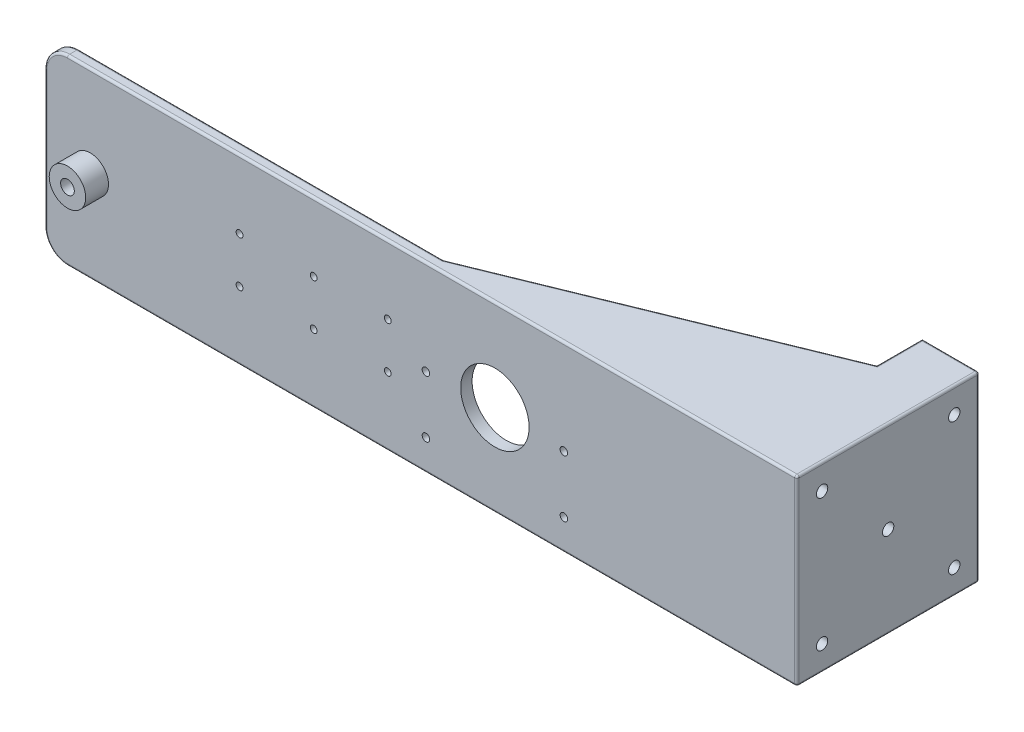
SolidWorks part; units mm, degrees
ref_plane "前视基准面" through (0, 0, 0) normal (0, 0, 1) x (1, 0, 0)
ref_plane "上视基准面" through (0, 0, 0) normal (0, 1, 0) x (1, 0, 0)
ref_plane "右视基准面" through (0, 0, 0) normal (1, 0, 0) x (0, 0, -1)
sketch "草图1" plane through (0, 0, 0) normal (0, 0, 1) x (1, 0, 0)
  line L1 (165, -40) -> (-165, -40)
  line L2 (165, -40) -> (165, 40)
  line L3 (165, 40) -> (-165, 40)
  line L4 (-165, -40) -> (-165, 40)
  line L5 (165, -40) -> (-165, 40) construction
  line L6 (165, 40) -> (-165, -40) construction
  point P0 (0, 0)
  dimension "D1" = 80
  dimension "D2" = 330
extrude "凸台-拉伸1" add sketch "草图1" along normal blind 5
sketch "草图2" plane through (0, 0, 5) normal (0, 0, 1) x (1, 0, 0)
  line L0 (-165, 40) -> (-165, -40) construction
  circle A0 centre (-145, 0) radius 5
  dimension "D1" = 10
  dimension "D2" = 20
extrude "切除-拉伸1" cut sketch "草图2" against normal blind 5
sketch "草图3" plane through (0, 0, 5) normal (0, 0, 1) x (1, 0, 0)
  circle A0 centre (-45, 0) radius 4
  dimension "D2" = 8
extrude "切除-拉伸2" cut sketch "草图3" against normal blind 10
sketch "草图4" plane through (0, 0, 5) normal (0, 0, 1) x (1, 0, 0)
  line L1 (-3, -10) -> (-91, -10)
  line L2 (-3, -10) -> (-3, 10)
  line L3 (-3, 10) -> (-91, 10)
  line L4 (-91, -10) -> (-91, 10)
  line L5 (-3, -10) -> (-91, 10) construction
  line L6 (-3, 10) -> (-91, -10) construction
  line L7 (-165, 40) -> (-165, -40) construction
  point P0 (-47, 0)
  dimension "D1" = 162
  dimension "D2" = 20
  dimension "D3" = 88
extrude "凸台-拉伸2" add sketch "草图4" along normal blind 10
sketch "草图5" plane through (0, 0, 5) normal (0, 0, 1) x (1, 0, 0)
  line L1 (-165, 40) -> (-165, -40) construction
  circle A0 centre (32.5, 0) radius 15
  dimension "D1" = 30
  dimension "D2" = 197.5
extrude "切除-拉伸3" cut sketch "草图5" against normal blind 10
sketch "草图6" plane through (0, 0, 0) normal (0, 0, -1) x (-1, 0, 0)
  circle A0 centre (145, 0) radius 8
  dimension "D1" = 16
extrude "凸台-拉伸3" add sketch "草图6" against normal blind 15
hole_wizard "Ø6.0mm 暗销孔1" positions "草图8" profile "草图9" hole size "Ø6.0" standard "GB" end condition through all
sketch "草图8" plane through (0, 0, 15) normal (0, 0, 1) x (1, 0, 0)
  point P0 (-145, 0)
sketch "草图9" plane through (-145, 0, 15) normal (1, 0, 0) x (0, -1, 0)
  line L0 (0, 0) -> (0, 15)
  line L1 (0, 15) -> (3, 15)
  line L2 (3, 15) -> (3, 0)
  line L5 (3, 0) -> (0, 0)
  line L11 (0, -6.35) -> (0, 107.95) construction
  dimension "通孔孔直径" = 6
  dimension "通孔孔深度" = 15
sketch "草图10" plane through (0, 0, 15) normal (0, 0, 1) x (1, 0, 0)
  line L0 (-91, 0) -> (-3, 0) construction
  line L1 (-91, 10) -> (-91, -10) construction
  line L2 (-3, -10) -> (-3, 10) construction
  line L3 (-91, 5.1) -> (-3, 5.1)
  line L4 (-91, -5.1) -> (-3, -5.1)
  arc A0 (-91, 5.1) -> (-91, -5.1) centre (-91, 0) ccw
  arc A1 (-3, -5.1) -> (-3, 5.1) centre (-3, 0) ccw
  point P6 (-47, 0)
  dimension "D1" = 5.1
extrude "切除-拉伸4" cut sketch "草图10" against normal blind 7
hole_wizard "M4 螺纹孔1" positions "草图11" profile "草图12" tap size "M4" standard "GB" end condition through all
sketch "草图11" plane through (0, 0, 0) normal (0, 0, -1) x (-1, 0, 0)
  point P0 (-2.25, -26.5)
  point P3 (-2.25, -1.5)
  point P6 (-62.75, -26.5)
  point P8 (-62.75, -1.5)
sketch "草图12" plane through (2.25, -26.5, 0) normal (1, 0, 0) x (0, 1, 0)
  line L0 (0, 0) -> (0, 15)
  line L1 (0, 15) -> (1.65, 15)
  line L2 (1.65, 15) -> (1.65, 0)
  line L5 (1.65, 0) -> (0, 0)
  line L11 (0, -6.35) -> (0, 107.95) construction
  dimension "通孔螺纹孔钻头直径" = 3.3
  dimension "通孔螺纹孔钻头深度" = 15
cosmetic thread "孔螺蚊线5" parameters "D2"=4
cosmetic thread "孔螺蚊线6" parameters "D2"=4
cosmetic thread "孔螺蚊线7" parameters "D2"=4
cosmetic thread "孔螺蚊线8" parameters "D2"=4
fillet "圆角1" radius 10 2 edges at (-165, -40, 2.5) (-165, 40, 2.5)
sketch "草图13" plane through (0, 0, 5) normal (0, 0, 1) x (1, 0, 0)
  circle A0 centre (-45, 0) radius 6.9694
extrude "凸台-拉伸5" add sketch "草图13" against normal blind 5
sketch "草图14" plane through (0, -40, 0) normal (0, -1, 0) x (1, 0, 0)
  line L1 (165, 0) -> (160, 0)
  line L2 (165, 0) -> (165, -75)
  line L3 (165, -75) -> (160, -75)
  line L4 (160, 0) -> (160, -75)
  dimension "D1" = 5
  dimension "D2" = 75
extrude "凸台-拉伸6" add sketch "草图14" against normal up to surface (80 mm away) up to face at (5, 40, 2.5)
sketch "草图15" plane through (0, -40, 0) normal (0, -1, 0) x (1, 0, 0)
  line L1 (160, -75) -> (140, -75)
  line L2 (160, -75) -> (160, -70)
  line L3 (160, -70) -> (140, -70)
  line L4 (140, -75) -> (140, -70)
  dimension "D1" = 5
  dimension "D2" = 20
extrude "凸台-拉伸7" add sketch "草图15" against normal up to surface (80 mm away) up to face at (56.6667, 40, -23.3333)
sketch "草图16" plane through (0, -40, 0) normal (0, -1, 0) x (1, 0, 0)
  line L0 (5, 5) -> (5, 0)
  line L1 (-155, 5) -> (165, 5) construction
  line L2 (-155, 0) -> (160, 0) construction
  line L4 (140, -75) -> (165, -75)
  line L5 (165, -75) -> (165, 5)
  line L6 (165, 5) -> (5, 5)
  line L7 (140, -75) -> (140, -55)
  line L8 (140, -55) -> (5, 0)
  dimension "D1" = 160
  dimension "D2" = 20
extrude "凸台-拉伸8" add sketch "草图16" against normal blind 5
mirror "镜向1" about plane through (0, 0, 0) normal (0, 1, 0) of "凸台-拉伸8"
sketch "草图17" plane through (0, 0, -75) normal (0, 0, -1) x (-1, 0, 0)
  line L0 (-165, 40) -> (-165, -40) construction
  circle A0 centre (-152, -15) radius 3
  circle A1 centre (-152, 15) radius 3
  dimension "D1" = 6
  dimension "D3" = 13
  dimension "D2" = 13
extrude "切除-拉伸5" cut sketch "草图17" against normal blind 5
fillet "圆角2" radius 1 20 edges at (-162.0711, 37.0711, 5) (-165, 0, 5) (-162.0711, -37.0711, 5) (-162.0711, 37.0711, 0) (-165, 0, 0) (-162.0711, -37.0711, 0) (5, 40, 5) (-75, 40, 0) (152.5, -40, -75) (152.5, 40, -75) (165, 0, -75) (165, 0, 5) (165, 40, -35) (5, -40, 5) (165, -40, -35) (-75, -40, 0) (72.5, 40, -27.5) (140, 40, -65) (140, -40, -65) (72.5, -40, -27.5)
fillet "圆角3" radius 1 4 edges at (-47, -10, 15) (-47, -5.1, 15) (-47, 5.1, 15) (-47, 10, 15)
sketch "草图18" plane through (-3, 0, 0) normal (1, 0, 0) x (0, 0, -1)
  line L8 (-15, -6.1) -> (-15, -9)
  line L9 (-14, -10) -> (-5, -10)
  line L10 (-5, -10) -> (-5, 10)
  line L11 (-5, 10) -> (-14, 10)
  line L12 (-15, 9) -> (-15, 6.1)
  line L13 (-14, 5.1) -> (-8, 5.1)
  line L14 (-8, 5.1) -> (-8, -5.1)
  line L15 (-8, -5.1) -> (-14, -5.1)
  line L16 (-15, -6.1) -> (-15, -9)
  line L17 (-14, -10) -> (-5, -10)
  line L18 (-5, -10) -> (-5, 10)
  line L19 (-5, 10) -> (-14, 10)
  line L20 (-15, 9) -> (-15, 6.1)
  line L21 (-14, 5.1) -> (-8, 5.1)
  line L22 (-8, 5.1) -> (-8, -5.1)
  line L23 (-8, -5.1) -> (-14, -5.1)
  arc A4 (-15, -9) -> (-14, -10) centre (-14, -9) ccw
  arc A5 (-14, 10) -> (-15, 9) centre (-14, 9) ccw
  arc A6 (-15, 6.1) -> (-14, 5.1) centre (-14, 6.1) ccw
  arc A7 (-14, -5.1) -> (-15, -6.1) centre (-14, -6.1) ccw
  arc A8 (-15, -9) -> (-14, -10) centre (-14, -9) ccw
  arc A9 (-14, 10) -> (-15, 9) centre (-14, 9) ccw
  arc A10 (-15, 6.1) -> (-14, 5.1) centre (-14, 6.1) ccw
  arc A11 (-14, -5.1) -> (-15, -6.1) centre (-14, -6.1) ccw
  dimension "D1" = 0
extrude "切除-拉伸6" cut sketch "草图18" against normal blind 100
hole_wizard "Ø3.0mm 暗销孔1" positions "草图19" profile "草图20" hole size "Ø3.0" standard "GB"
sketch "草图19" plane through (0, 0, 5) normal (0, 0, 1) x (1, 0, 0)
  point P0 (-14.5, -10)
  point P3 (-14.5, 10)
  point P6 (-47, 10)
  point P9 (-47, -10)
  point P12 (-79.5, -10)
  point P15 (-79.5, 10)
sketch "草图20" plane through (-14.5, -10, 5) normal (1, 0, 0) x (0, -1, 0)
  line L0 (0, 0) -> (0, 8.4013)
  line L1 (0, 8.4013) -> (1.5, 7.5)
  line L2 (1.5, 7.5) -> (1.5, 0)
  line L5 (1.5, 0) -> (0, 0)
  line L10 (0, 8.4013) -> (-1.5, 7.5) construction
  line L11 (0, -6.35) -> (0, 107.95) construction
  dimension "孔直径" = 3
  dimension "孔深度" = 7.5
  dimension "导头角度" = 118
sketch "草图21" plane through (165, 0, 0) normal (1, 0, 0) x (0, 0, -1)
  line L0 (35, 40) -> (35, -40) construction
  line L1 (-4, 40) -> (74, 40) construction
  line L2 (74, -40) -> (-4, -40) construction
  circle A0 centre (35, 0) radius 2.5
  dimension "D1" = 5
extrude "切除-拉伸7" cut sketch "草图21" against normal blind 10
sketch "草图22" plane through (165, 0, 0) normal (1, 0, 0) x (0, 0, -1)
  line L0 (6.0086, 28.9914) -> (35, 0) construction
  line L1 (35, 0) -> (35, 41) construction
  circle A0 centre (35, 0) radius 41 construction
  dimension "D1" = 82
  dimension "D2" = 45
hole_wizard "Ø5.0mm 暗销孔1" positions "草图23" profile "草图24" hole size "Ø5.0" standard "GB"
sketch "草图23" plane through (165, 0, 0) normal (1, 0, 0) x (0, 0, -1)
  point P0 (6.0086, 28.9914)
sketch "草图24" plane through (165, 28.9914, -6.0086) normal (0, 1, 0) x (0, 0, -1)
  line L0 (0, 0) -> (0, 13.9022)
  line L1 (0, 13.9022) -> (2.5, 12.4)
  line L2 (2.5, 12.4) -> (2.5, 0)
  line L5 (2.5, 0) -> (0, 0)
  line L10 (0, 13.9022) -> (-2.5, 12.4) construction
  line L11 (0, -6.35) -> (0, 107.95) construction
  dimension "孔直径" = 5
  dimension "孔深度" = 12.4
  dimension "导头角度" = 118
pattern_circular "阵列(圆周)1" count 4 over 360 about axis through (0, 0, -35) along (1, 0, 0) of "Ø5.0mm 暗销孔1"
sketch "草图25" plane through (0, 0, 15) normal (0, 0, 1) x (1, 0, 0)
  circle A0 centre (-145, 0) radius 5.25
  dimension "D1" = 10.5
extrude "切除-拉伸8" cut sketch "草图25" against normal through all from offset 5
